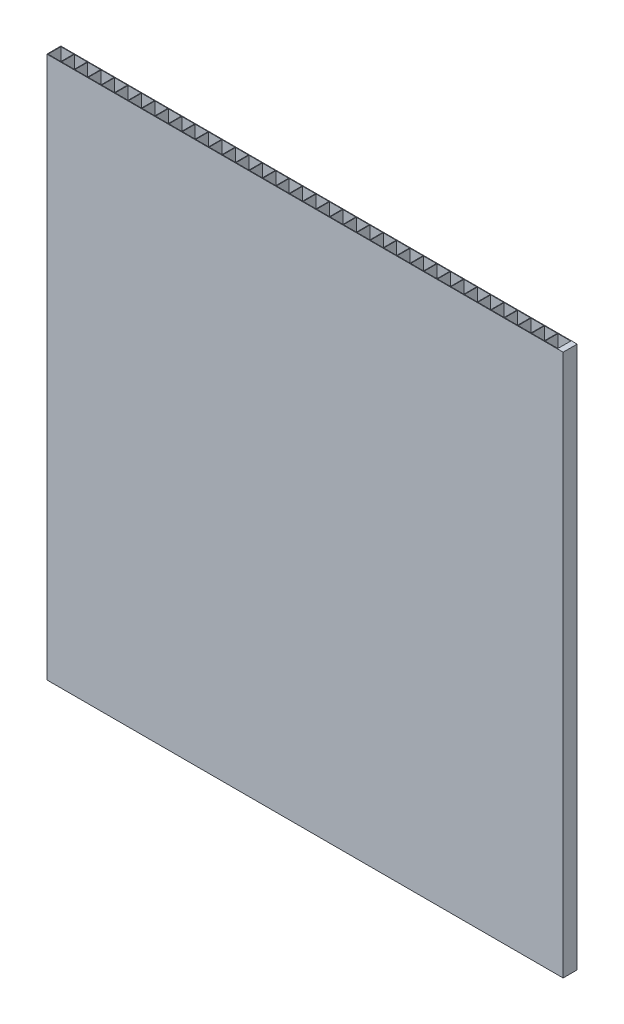
SolidWorks part; units mm, degrees
material "Perspex (TM) GS Acrylic Cast Sheet"
ref_plane "Front Plane" through (0, 0, 0) normal (0, 0, 1) x (1, 0, 0)
ref_plane "Top Plane" through (0, 0, 0) normal (0, 1, 0) x (1, 0, 0)
ref_plane "Right Plane" through (0, 0, 0) normal (1, 0, 0) x (0, 0, -1)
sketch "Sketch1" plane through (0, 0, 0) normal (0, 1, 0) x (1, 0, 0)
  line L0 (6, 5.75) -> (6, 0.25)
  line L1 (0, 0) -> (221, 0)
  line L2 (0, 0) -> (0, 6)
  line L3 (0, 6) -> (221, 6)
  line L4 (221, 0) -> (221, 6)
  line L5 (0.25, 5.75) -> (5.75, 5.75)
  line L6 (0.25, 5.75) -> (0.25, 0.25)
  line L7 (0.25, 0.25) -> (5.75, 0.25)
  line L8 (5.75, 5.75) -> (5.75, 0.25)
  line L9 (6, 5.75) -> (11.5, 5.75)
  line L10 (11.5, 5.75) -> (11.5, 0.25)
  line L11 (6, 0.25) -> (11.5, 0.25)
  line L12 (11.75, 5.75) -> (11.75, 0.25)
  line L13 (11.75, 5.75) -> (17.25, 5.75)
  line L14 (17.25, 5.75) -> (17.25, 0.25)
  line L15 (11.75, 0.25) -> (17.25, 0.25)
  line L16 (17.5, 5.75) -> (17.5, 0.25)
  line L17 (17.5, 5.75) -> (23, 5.75)
  line L18 (23, 5.75) -> (23, 0.25)
  line L19 (17.5, 0.25) -> (23, 0.25)
  line L20 (23.25, 5.75) -> (23.25, 0.25)
  line L21 (23.25, 5.75) -> (28.75, 5.75)
  line L22 (28.75, 5.75) -> (28.75, 0.25)
  line L23 (23.25, 0.25) -> (28.75, 0.25)
  line L24 (29, 5.75) -> (29, 0.25)
  line L25 (29, 5.75) -> (34.5, 5.75)
  line L26 (34.5, 5.75) -> (34.5, 0.25)
  line L27 (29, 0.25) -> (34.5, 0.25)
  line L28 (34.75, 5.75) -> (34.75, 0.25)
  line L29 (34.75, 5.75) -> (40.25, 5.75)
  line L30 (40.25, 5.75) -> (40.25, 0.25)
  line L31 (34.75, 0.25) -> (40.25, 0.25)
  line L32 (40.5, 5.75) -> (40.5, 0.25)
  line L33 (40.5, 5.75) -> (46, 5.75)
  line L34 (46, 5.75) -> (46, 0.25)
  line L35 (40.5, 0.25) -> (46, 0.25)
  line L36 (46.25, 5.75) -> (46.25, 0.25)
  line L37 (46.25, 5.75) -> (51.75, 5.75)
  line L38 (51.75, 5.75) -> (51.75, 0.25)
  line L39 (46.25, 0.25) -> (51.75, 0.25)
  line L40 (52, 5.75) -> (52, 0.25)
  line L41 (52, 5.75) -> (57.5, 5.75)
  line L42 (57.5, 5.75) -> (57.5, 0.25)
  line L43 (52, 0.25) -> (57.5, 0.25)
  line L44 (57.75, 5.75) -> (57.75, 0.25)
  line L45 (57.75, 5.75) -> (63.25, 5.75)
  line L46 (63.25, 5.75) -> (63.25, 0.25)
  line L47 (57.75, 0.25) -> (63.25, 0.25)
  line L48 (63.5, 5.75) -> (63.5, 0.25)
  line L49 (63.5, 5.75) -> (69, 5.75)
  line L50 (69, 5.75) -> (69, 0.25)
  line L51 (63.5, 0.25) -> (69, 0.25)
  line L52 (69.25, 5.75) -> (69.25, 0.25)
  line L53 (69.25, 5.75) -> (74.75, 5.75)
  line L54 (74.75, 5.75) -> (74.75, 0.25)
  line L55 (69.25, 0.25) -> (74.75, 0.25)
  line L56 (75, 5.75) -> (75, 0.25)
  line L57 (75, 5.75) -> (80.5, 5.75)
  line L58 (80.5, 5.75) -> (80.5, 0.25)
  line L59 (75, 0.25) -> (80.5, 0.25)
  line L60 (80.75, 5.75) -> (80.75, 0.25)
  line L61 (80.75, 5.75) -> (86.25, 5.75)
  line L62 (86.25, 5.75) -> (86.25, 0.25)
  line L63 (80.75, 0.25) -> (86.25, 0.25)
  line L64 (86.5, 5.75) -> (86.5, 0.25)
  line L65 (86.5, 5.75) -> (92, 5.75)
  line L66 (92, 5.75) -> (92, 0.25)
  line L67 (86.5, 0.25) -> (92, 0.25)
  line L68 (92.25, 5.75) -> (92.25, 0.25)
  line L69 (92.25, 5.75) -> (97.75, 5.75)
  line L70 (97.75, 5.75) -> (97.75, 0.25)
  line L71 (92.25, 0.25) -> (97.75, 0.25)
  line L72 (98, 5.75) -> (98, 0.25)
  line L73 (98, 5.75) -> (103.5, 5.75)
  line L74 (103.5, 5.75) -> (103.5, 0.25)
  line L75 (98, 0.25) -> (103.5, 0.25)
  line L76 (103.75, 5.75) -> (103.75, 0.25)
  line L77 (103.75, 5.75) -> (109.25, 5.75)
  line L78 (109.25, 5.75) -> (109.25, 0.25)
  line L79 (103.75, 0.25) -> (109.25, 0.25)
  line L80 (109.5, 5.75) -> (109.5, 0.25)
  line L81 (109.5, 5.75) -> (115, 5.75)
  line L82 (115, 5.75) -> (115, 0.25)
  line L83 (109.5, 0.25) -> (115, 0.25)
  line L84 (115.25, 5.75) -> (115.25, 0.25)
  line L85 (115.25, 5.75) -> (120.75, 5.75)
  line L86 (120.75, 5.75) -> (120.75, 0.25)
  line L87 (115.25, 0.25) -> (120.75, 0.25)
  line L88 (121, 5.75) -> (121, 0.25)
  line L89 (121, 5.75) -> (126.5, 5.75)
  line L90 (126.5, 5.75) -> (126.5, 0.25)
  line L91 (121, 0.25) -> (126.5, 0.25)
  line L92 (126.75, 5.75) -> (126.75, 0.25)
  line L93 (126.75, 5.75) -> (132.25, 5.75)
  line L94 (132.25, 5.75) -> (132.25, 0.25)
  line L95 (126.75, 0.25) -> (132.25, 0.25)
  line L96 (132.5, 5.75) -> (132.5, 0.25)
  line L97 (132.5, 5.75) -> (138, 5.75)
  line L98 (138, 5.75) -> (138, 0.25)
  line L99 (132.5, 0.25) -> (138, 0.25)
  line L100 (138.25, 5.75) -> (138.25, 0.25)
  line L101 (138.25, 5.75) -> (143.75, 5.75)
  line L102 (143.75, 5.75) -> (143.75, 0.25)
  line L103 (138.25, 0.25) -> (143.75, 0.25)
  line L104 (144, 5.75) -> (144, 0.25)
  line L105 (144, 5.75) -> (149.5, 5.75)
  line L106 (149.5, 5.75) -> (149.5, 0.25)
  line L107 (144, 0.25) -> (149.5, 0.25)
  line L108 (149.75, 5.75) -> (149.75, 0.25)
  line L109 (149.75, 5.75) -> (155.25, 5.75)
  line L110 (155.25, 5.75) -> (155.25, 0.25)
  line L111 (149.75, 0.25) -> (155.25, 0.25)
  line L112 (155.5, 5.75) -> (155.5, 0.25)
  line L113 (155.5, 5.75) -> (161, 5.75)
  line L114 (161, 5.75) -> (161, 0.25)
  line L115 (155.5, 0.25) -> (161, 0.25)
  line L116 (161.25, 5.75) -> (161.25, 0.25)
  line L117 (161.25, 5.75) -> (166.75, 5.75)
  line L118 (166.75, 5.75) -> (166.75, 0.25)
  line L119 (161.25, 0.25) -> (166.75, 0.25)
  line L120 (167, 5.75) -> (167, 0.25)
  line L121 (167, 5.75) -> (172.5, 5.75)
  line L122 (172.5, 5.75) -> (172.5, 0.25)
  line L123 (167, 0.25) -> (172.5, 0.25)
  line L124 (172.75, 5.75) -> (172.75, 0.25)
  line L125 (172.75, 5.75) -> (178.25, 5.75)
  line L126 (178.25, 5.75) -> (178.25, 0.25)
  line L127 (172.75, 0.25) -> (178.25, 0.25)
  line L128 (178.5, 5.75) -> (178.5, 0.25)
  line L129 (178.5, 5.75) -> (184, 5.75)
  line L130 (184, 5.75) -> (184, 0.25)
  line L131 (178.5, 0.25) -> (184, 0.25)
  line L132 (184.25, 5.75) -> (184.25, 0.25)
  line L133 (184.25, 5.75) -> (189.75, 5.75)
  line L134 (189.75, 5.75) -> (189.75, 0.25)
  line L135 (184.25, 0.25) -> (189.75, 0.25)
  line L136 (190, 5.75) -> (190, 0.25)
  line L137 (190, 5.75) -> (195.5, 5.75)
  line L138 (195.5, 5.75) -> (195.5, 0.25)
  line L139 (190, 0.25) -> (195.5, 0.25)
  line L140 (195.75, 5.75) -> (195.75, 0.25)
  line L141 (195.75, 5.75) -> (201.25, 5.75)
  line L142 (201.25, 5.75) -> (201.25, 0.25)
  line L143 (195.75, 0.25) -> (201.25, 0.25)
  line L144 (201.5, 5.75) -> (201.5, 0.25)
  line L145 (201.5, 5.75) -> (207, 5.75)
  line L146 (207, 5.75) -> (207, 0.25)
  line L147 (201.5, 0.25) -> (207, 0.25)
  line L148 (207.25, 5.75) -> (207.25, 0.25)
  line L149 (207.25, 5.75) -> (212.75, 5.75)
  line L150 (212.75, 5.75) -> (212.75, 0.25)
  line L151 (207.25, 0.25) -> (212.75, 0.25)
  line L152 (213, 5.75) -> (213, 0.25)
  line L153 (213, 5.75) -> (218.5, 5.75)
  line L154 (218.5, 5.75) -> (218.5, 0.25)
  line L155 (213, 0.25) -> (218.5, 0.25)
  line L156 (218.75, 5.75) -> (218.75, 0.25)
  line L157 (218.75, 5.75) -> (224.25, 5.75)
  line L158 (224.25, 5.75) -> (224.25, 0.25)
  line L159 (218.75, 0.25) -> (224.25, 0.25)
  point P9 (0.25, 3)
  point P10 (0, 3)
  dimension "D1" = 221
  dimension "D2" = 6
  dimension "D3" = 5.5
  dimension "D4" = 5.5
  dimension "D5" = 0.25
  dimension "D6" = 39
extrude "Boss-Extrude1" add sketch "Sketch1" along normal blind 232 contours L1 L4 L3 L2 | L8 L7 L6 L5 | L0 L11 L10 L9 | L12 L15 L14 L13 | L16 L19 L18 L17 | L20 L23 L22 L21 | L26 L27 L24 L25 | L28 L31 L30 L29 | L32 L35 L34 L33 | L38 L39 L36 L37 | L40 L43 L42 L41 | L46 L47 L44 L45 | L50 L51 L48 L49 | L52 L55 L54 L53 | L56 L59 L58 L57 | L60 L63 L62 L61 | L67 L66 L65 L64 | L71 L70 L69 L68 | L75 L74 L73 L72 | L79 L78 L77 L76 | L83 L82 L81 L80 | L87 L86 L85 L84 | L91 L90 L89 L88 | L94 L95 L92 L93 | L96 L99 L98 L97 | L100 L103 L102 L101 | L104 L107 L106 L105 | L108 L111 L110 L109 | L112 L115 L114 L113 | L116 L119 L118 L117 | L122 L123 L120 L121 | L124 L127 L126 L125 | L128 L131 L130 L129 | L132 L135 L134 L133 | L136 L139 L138 L137 | L140 L143 L142 L141 | L144 L147 L146 L145 | L148 L151 L150 L149 | L152 L155 L154 L153
